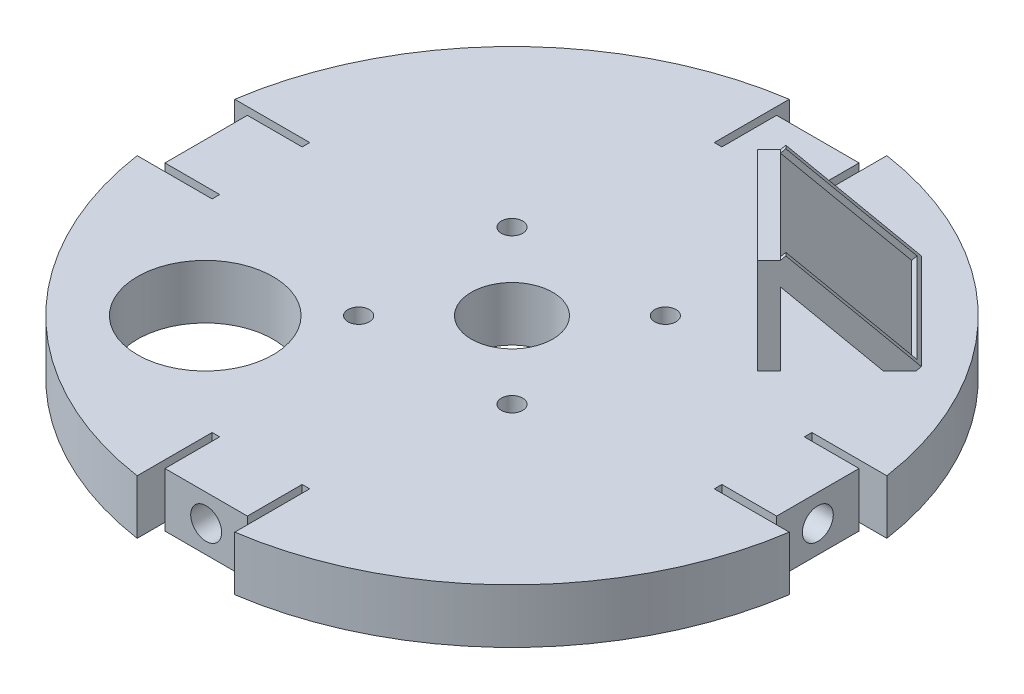
SolidWorks part; units mm, degrees
ref_plane "Front Plane" through (0, 0, 0) normal (0, 0, 1) x (1, 0, 0)
ref_plane "Top Plane" through (0, 0, 0) normal (0, 1, 0) x (1, 0, 0)
ref_plane "Right Plane" through (0, 0, 0) normal (1, 0, 0) x (0, 0, -1)
sketch "Sketch2" plane through (0, 0, 0) normal (1, 0, 0) x (0, 0, -1)
  line L0 (0, 9.4343) -> (0, -5.6606) construction
  line L1 (9.525, -6.35) -> (77.216, -6.35)
  line L2 (9.525, -6.35) -> (9.525, 6.35)
  line L3 (9.525, 6.35) -> (77.216, 6.35)
  line L4 (77.216, -6.35) -> (77.216, 6.35)
  line L5 (0, 0) -> (17.4231, 0) construction
  dimension "D1" = 12.7
  dimension "D2" = 19.05
  dimension "D3" = 154.432
revolve "Revolve1" add sketch "Sketch2" angle 360 about L0
sketch "Sketch3" plane through (0, 6.35, 0) normal (0, 1, 0) x (1, 0, 0)
  line L0 (0, 0) -> (17.9605, 17.9605) construction
  line L1 (0, 0) -> (13.035, 0) construction
  circle A0 centre (17.9605, 17.9605) radius 2.5019
  dimension "D3" = 5.0038
  dimension "D1" = 25.4
  dimension "D2" = 45
extrude "Cut-Extrude1" cut sketch "Sketch3" against normal through all contours A0
sketch "Sketch4" plane through (0, 6.35, 0) normal (0, 1, 0) x (1, 0, 0)
  line L0 (17.9605, 17.9605) -> (17.9605, -17.9605) construction
  line L1 (17.9605, -17.9605) -> (-17.9605, 17.9605) construction
  line L2 (-17.9605, 17.9605) -> (17.9605, 17.9605) construction
pattern_linear "LPattern1" count 2 spacing 35.921 along (0, 0, 1) count 2 spacing 35.921 along (-1, 0, 0) of "Cut-Extrude1"
sketch "Sketch5" plane through (0, 6.35, 0) normal (0, 1, 0) x (1, 0, 0)
  line L0 (0, 0) -> (0, -51.3071) construction
  line L1 (0, 0) -> (-35.921, -35.921)
  circle A0 centre (-35.921, -35.921) radius 15.875
  dimension "D3" = 31.75
  dimension "D1" = 45
  dimension "D2" = 50.8
extrude "Cut-Extrude2" cut sketch "Sketch5" against normal through all
sketch "Sketch6" plane through (0, 6.35, 0) normal (0, 1, 0) x (1, 0, 0)
  line L0 (0, 0) -> (54.6, 54.6)
  line L1 (0, 0) -> (18.1357, 0)
  circle A0 centre (0, 0) radius 77.216 construction
  dimension "D1" = 45
ref_plane "Plane1" through (0, 0, 0) normal (0.7071, 0, 0.7071) x (0.7071, 0, -0.7071)
sketch "Sketch7" plane through (0, 0, 0) normal (0.7071, 0, 0.7071) x (0.7071, 0, -0.7071)
  line L0 (0, 6.35) -> (44.45, 6.35) construction
  line L1 (77.216, 6.35) -> (-77.216, 6.35) construction
  line L2 (66.9006, 6.35) -> (44.45, 28.8006)
  line L3 (44.45, 28.8006) -> (40.64, 28.8006)
  line L4 (40.64, 28.8006) -> (40.64, 6.35)
  line L5 (0, 6.35) -> (0, 0) construction
  line L6 (44.45, 6.35) -> (44.45, 23.4125)
  line L7 (44.45, 23.4125) -> (61.5125, 6.35)
  line L8 (61.5125, 6.35) -> (66.9006, 6.35)
  line L9 (40.64, 6.35) -> (44.45, 6.35)
  dimension "D1" = 40.64
  dimension "D2" = 45
  dimension "D3" = 31.75
  dimension "D4" = 3.81
  dimension "D5" = 3.81
extrude "Boss-Extrude1" add sketch "Sketch7" along normal mid plane 31.75
sketch "Sketch8" plane through (25.898, 36.6253, -25.898) normal (0.5, 0.7071, -0.5) x (0.866, -0.4082, 0.2887)
  line L0 (6.3888, 9.0352) -> (24.1331, 34.1294) construction
  line L1 (19.3507, -0.1303) -> (-6.5731, 18.2006) construction
  line L2 (37.6816, 25.7935) -> (11.7578, 44.1244) construction
  line L3 (37.6816, 25.7935) -> (19.3507, -0.1303) construction
  line L4 (11.7578, 44.1244) -> (-6.5731, 18.2006) construction
  line L5 (37.6816, 25.7935) -> (11.7578, 44.1244)
  line L6 (37.6816, 25.7935) -> (19.3507, -0.1303)
  line L8 (11.7578, 44.1244) -> (-6.5731, 18.2006)
  line L9 (36.2654, 25.5505) -> (12.0008, 42.7082)
  line L10 (12.0008, 42.7082) -> (-5.1569, 18.4436)
  line L12 (36.2654, 25.5505) -> (19.1077, 1.2859)
  line L13 (19.1077, 1.2859) -> (-5.1569, 18.4436) construction
  line L14 (19.3507, -0.1303) -> (-6.5731, 18.2006) construction
  line L15 (-5.1569, 18.4436) -> (-5.7435, 17.614)
  line L16 (-5.7435, 17.614) -> (-6.5731, 18.2006)
  line L17 (19.1077, 1.2859) -> (18.5211, 0.4563)
  line L18 (18.5211, 0.4563) -> (19.3507, -0.1303)
  dimension "D1" = 1.016
extrude "Boss-Extrude2" add sketch "Sketch8" along normal mid plane 2.54 contours L6 L18 L17 L12 L9 L10 L15 L16 L8 L5
sketch "Sketch9" plane through (0, 6.35, 0) normal (0, 1, 0) x (1, 0, 0)
  line L0 (0, 0) -> (43.1052, -43.1052) construction
  line L1 (0, 0) -> (9.525, 0) construction
  line L2 (38.6151, -47.5954) -> (47.5954, -38.6151)
  line L3 (47.5954, -38.6151) -> (51.1875, -42.2072)
  line L4 (51.1875, -42.2072) -> (42.2072, -51.1875)
  line L5 (42.2072, -51.1875) -> (38.6151, -47.5954)
  circle A0 centre (0, 0) radius 9.525 construction
  dimension "D1" = 45
  dimension "D2" = 12.7
  dimension "D3" = 5.08
  dimension "D4" = 60.96
extrude "Boss-Extrude3" [suppressed] add sketch "Sketch9" along normal blind 127
fillet "Fillet1" [suppressed] radius 5.08
sketch "Sketch10" [suppressed] plane through (43.1052, 0, 43.1052) normal (-0.7071, 0, -0.7071) x (-0.7071, 0, 0.7071)
  line L0 (0, 133.35) -> (0, 128.0481)
  line L1 (-6.35, 133.35) -> (6.35, 133.35) construction
sketch "Sketch11" plane through (0, -6.35, 0) normal (0, -1, 0) x (-1, 0, 0)
  line L0 (0, 0) -> (-77.216, 0)
  circle A0 centre (0, 0) radius 77.216 construction
sketch "Sketch12" plane through (0, 6.35, 0) normal (0, 1, 0) x (1, 0, 0)
  line L0 (73.406, -11.43) -> (58.801, -11.43) construction
  line L1 (58.801, -11.43) -> (58.801, -9.652) construction
  line L2 (58.801, -9.652) -> (71.628, -9.652) construction
  line L3 (71.628, -9.652) -> (71.628, 9.652) construction
  line L4 (71.628, 9.652) -> (58.801, 9.652) construction
  line L5 (58.801, 9.652) -> (58.801, 11.43) construction
  line L6 (58.801, 11.43) -> (73.406, 11.43) construction
  line L7 (73.406, 11.43) -> (73.406, -11.43) construction
  line L8 (73.406, -11.43) -> (58.801, -11.43)
  line L9 (58.801, -11.43) -> (58.801, -9.652)
  line L10 (58.801, -9.652) -> (71.628, -9.652)
  line L11 (71.628, -9.652) -> (71.628, 9.652)
  line L12 (71.628, 9.652) -> (58.801, 9.652)
  line L13 (58.801, 9.652) -> (58.801, 11.43)
  line L14 (58.801, 11.43) -> (73.406, 11.43)
  line L15 (73.406, 11.43) -> (73.406, -11.43)
extrude "Cut-Extrude3" cut sketch "Sketch12" against normal through all
ref_plane "Plane2" through (77.216, 0, 0) normal (1, 0, 0) x (0, 0, -1)
sketch "Sketch13" plane through (77.216, 0, 0) normal (1, 0, 0) x (0, 0, -1)
  circle A0 centre (0, 0) radius 4.5847 construction
  circle A1 centre (0, 0) radius 4.5847 construction
  circle A2 centre (0, 0) radius 4.8387
  dimension "D1" = 0.254
extrude "Cut-Extrude4" cut sketch "Sketch13" against normal up to surface (3.81 mm away)
sketch "Sketch14" plane through (71.628, 0, 0) normal (1, 0, 0) x (0, 0, -1)
  circle A0 centre (0, 0) radius 3.6195
  dimension "D1" = 7.239
extrude "Cut-Extrude5" cut sketch "Sketch14" against normal blind 5.715
sketch "Sketch15" plane through (0, 6.35, 0) normal (0, 1, 0) x (1, 0, 0)
  line L0 (73.406, 11.43) -> (76.3653, 11.43)
  line L1 (73.406, -11.43) -> (76.3653, -11.43)
  line L2 (73.406, -11.43) -> (73.406, 11.43) construction
  line L3 (73.406, -11.43) -> (73.406, 11.43)
  circle A0 centre (0, 0) radius 77.216 construction
  arc A1 (76.3653, -11.43) -> (76.3653, 11.43) centre (0, 0) ccw
extrude "Cut-Extrude6" cut sketch "Sketch15" against normal through all
sketch "Sketch16" plane through (65.913, 0, 0) normal (1, 0, 0) x (0, 0, -1)
  circle A0 centre (0, 0) radius 2.413
  dimension "D1" = 4.826
extrude "Cut-Extrude7" cut sketch "Sketch16" against normal blind 2.54
pattern_circular "CirPattern2" count 4 over 360 about axis through (0, 0, 0) along (0, 1, 0) of "Cut-Extrude5", "Cut-Extrude4", "Cut-Extrude3", "Cut-Extrude6", "Cut-Extrude7"
